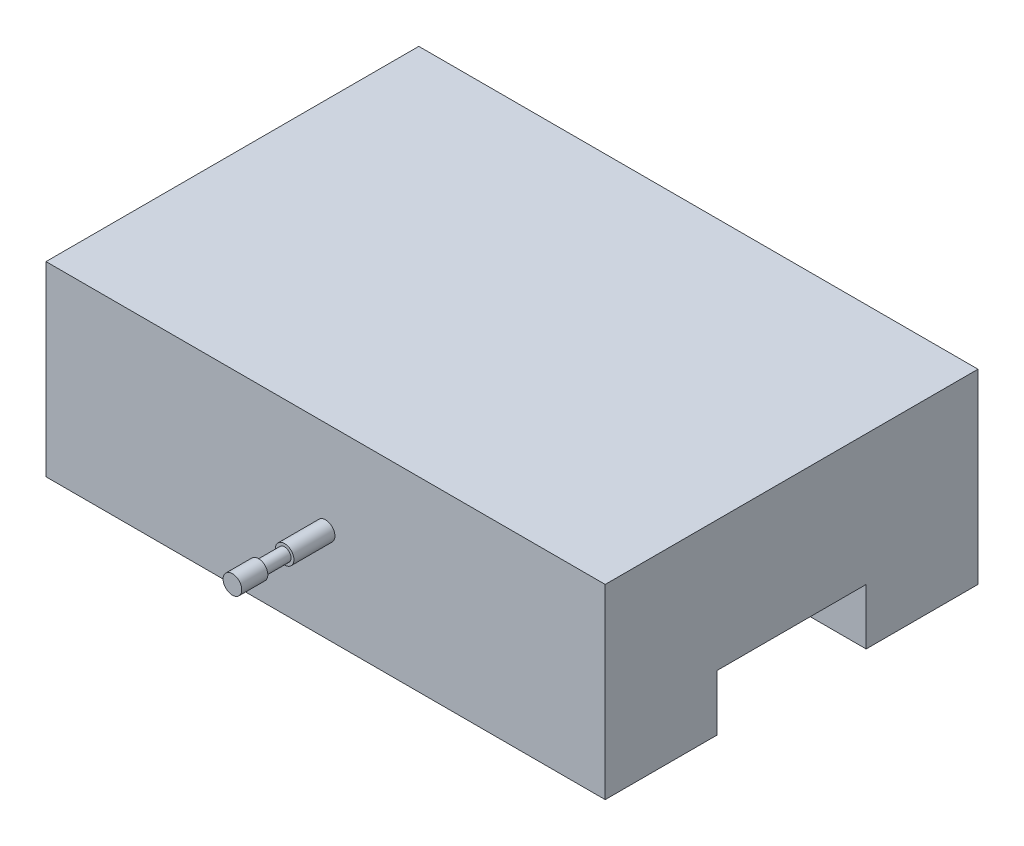
SolidWorks part; units mm, degrees
ref_plane "Front Plane" through (0, 0, 0) normal (0, 0, 1) x (1, 0, 0)
ref_plane "Top Plane" through (0, 0, 0) normal (0, 1, 0) x (1, 0, 0)
ref_plane "Right Plane" through (0, 0, 0) normal (1, 0, 0) x (0, 0, -1)
sketch "Sketch1" plane through (0, 0, 0) normal (1, 0, 0) x (0, 0, -1)
  line L0 (0, 99.9318) -> (0, -75.0709) construction
  line L5 (-50, 35) -> (50, 35)
  line L6 (-50, 35) -> (-50, -15)
  line L8 (50, 35) -> (50, -15)
  line L9 (100.4687, 0) -> (-99.8442, 0) construction
  line L10 (-50, -15) -> (-20, -15)
  line L11 (-20, -15) -> (-20, 0)
  line L12 (-20, 0) -> (20, 0)
  line L13 (20, 0) -> (20, -15)
  line L14 (20, -15) -> (50, -15)
  dimension "D1" = 100
  dimension "D2" = 50
  dimension "D3" = 30
  dimension "D4" = 15
extrude "Boss-Extrude1" add sketch "Sketch1" against normal blind 150
sketch "Sketch2" plane through (0, 0, 50) normal (0, 0, 1) x (1, 0, 0)
  line L0 (-150, 35) -> (0, 35) construction
  line L1 (0, 35) -> (0, -15) construction
  circle A0 centre (-75, 10) radius 2.5
  point P4 (0, 0)
  point P6 (-70.0552, 9.2591)
  dimension "D1" = 25
  dimension "D3" = 5
  dimension "D2" = 75
extrude "Boss-Extrude2" add sketch "Sketch2" along normal blind 25
sketch "Sketch3" plane through (0, 0, 75) normal (0, 0, 1) x (1, 0, 0)
  circle A0 centre (-75, 10) radius 2.5
  circle A1 centre (-75, 10) radius 1.7339
extrude "Cut-Extrude1" cut sketch "Sketch3" against normal blind 7 from offset 7
